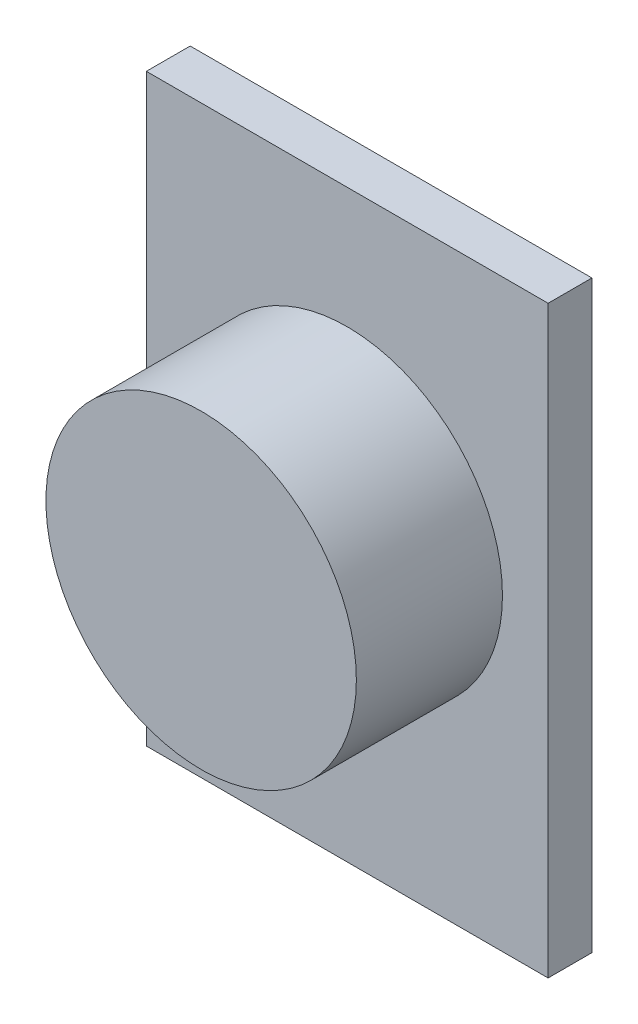
SolidWorks part; units mm, degrees
ref_plane "Front Plane" through (0, 0, 0) normal (0, 0, 1) x (1, 0, 0)
ref_plane "Top Plane" through (0, 0, 0) normal (0, 1, 0) x (1, 0, 0)
ref_plane "Right Plane" through (0, 0, 0) normal (1, 0, 0) x (0, 0, -1)
sketch "Sketch1" plane through (0, 0, 0) normal (0, 0, 1) x (1, 0, 0)
  line L0 (0, 14.3268) -> (0, -20.915) construction
  line L1 (-5.5, 8) -> (5.5, 8)
  line L2 (-5.5, 8) -> (-5.5, -8)
  line L3 (-5.5, -8) -> (5.5, -8)
  line L4 (5.5, 8) -> (5.5, -8)
  line L5 (-12.7059, 0) -> (25.7778, 0) construction
  dimension "D1" = 16
  dimension "D2" = 11
extrude "Boss-Extrude1" add sketch "Sketch1" along normal blind 1.2
sketch "Sketch2" plane through (0, 0, 1.2) normal (0, 0, 1) x (1, 0, 0)
  line L0 (0, 0) -> (0, 8.6768) construction
  circle A0 centre (0, 0.4435) radius 4.25
  point P2 (0, 0)
  point P6 (0, 0.4435)
  dimension "D1" = 8.5
extrude "Boss-Extrude2" add sketch "Sketch2" along normal blind 4
